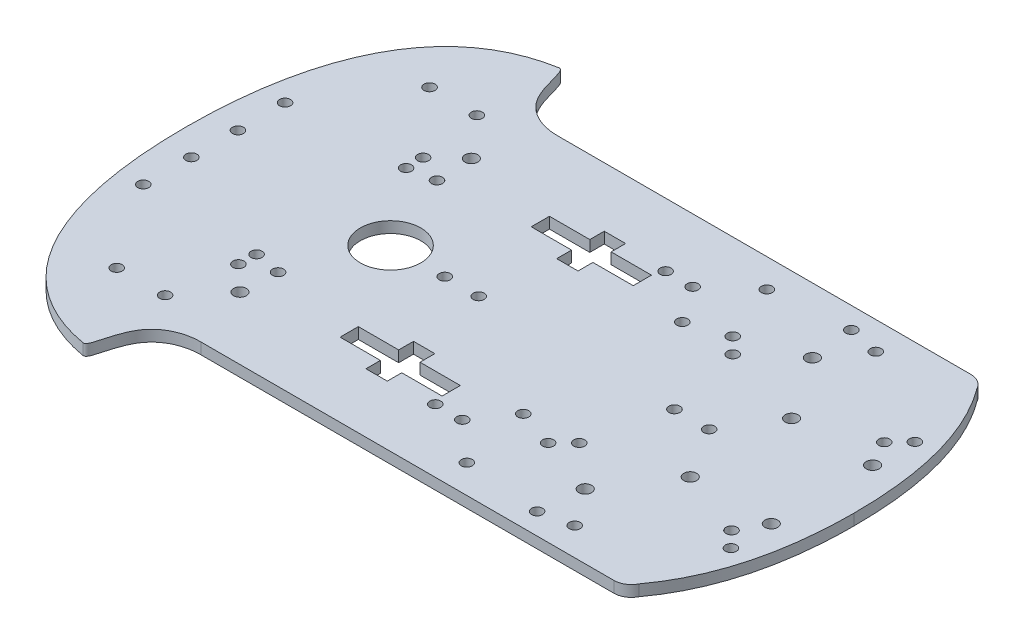
SolidWorks part; units mm, degrees
ref_plane "Front Plane" through (0, 0, 0) normal (0, 0, 1) x (1, 0, 0)
ref_plane "Top Plane" through (0, 0, 0) normal (0, 1, 0) x (1, 0, 0)
ref_plane "Right Plane" through (0, 0, 0) normal (1, 0, 0) x (0, 0, -1)
sketch "Sketch3" plane through (0, 0, 0) normal (0, 1, 0) x (1, 0, 0)
  line L0 (97.5968, 74.8054) -> (92.9104, -30.4241) construction
  line L1 (0, 0) -> (121.1912, 0) construction
  line L2 (11.94, 30.9929) -> (0, 30.9929)
  line L3 (11.94, -30.9929) -> (0, -30.9929)
  line L4 (0, 30.9929) -> (0, 25.5929)
  line L5 (0, -30.9929) -> (0, -25.5929)
  line L6 (0, 25.5929) -> (11.94, 25.5929)
  line L7 (0, -25.5929) -> (11.94, -25.5929)
  line L8 (11.94, 25.5929) -> (11.94, 21.1924)
  line L9 (11.94, -25.5929) -> (11.94, -21.1924)
  line L10 (11.94, 21.1924) -> (18.26, 21.1924)
  line L11 (11.94, -21.1924) -> (18.26, -21.1924)
  line L12 (18.26, 21.1924) -> (18.26, 25.5929)
  line L13 (18.26, -21.1924) -> (18.26, -25.5929)
  line L14 (18.26, 25.5929) -> (30.2, 25.5929)
  line L15 (18.26, -25.5929) -> (30.2, -25.5929)
  line L16 (30.2, 25.5929) -> (30.2, 30.9929)
  line L17 (30.2, -25.5929) -> (30.2, -30.9929)
  line L18 (30.2, 30.9929) -> (18.26, 30.9929)
  line L19 (30.2, -30.9929) -> (18.26, -30.9929)
  line L20 (18.26, 30.9929) -> (18.26, 35.2739)
  line L21 (18.26, -30.9929) -> (18.26, -35.2739)
  line L22 (18.26, 35.2739) -> (11.94, 35.2739)
  line L23 (18.26, -35.2739) -> (11.94, -35.2739)
  line L24 (11.94, 35.2739) -> (11.94, 30.9929)
  line L25 (11.94, -35.2739) -> (11.94, -30.9929)
  line L26 (0, 0) -> (-76.7012, 0) construction
  line L27 (87.6662, 15) -> (87.6662, -15) construction
  line L28 (87.6662, -15) -> (111.6662, -15) construction
  line L29 (111.6662, -15) -> (111.6662, 15) construction
  line L30 (111.6662, 15) -> (87.6662, 15) construction
  line L31 (31.2849, -34.0983) -> (39.2849, -34.0983) construction
  line L32 (-76.7012, 0) -> (-76.7012, -20.9854) construction
  line L33 (-36.6507, 70.4667) -> (-12.2251, 74.7655) construction
  line L34 (-19.4127, 52.8292) -> (102.905, 52.8292)
  line L35 (121.1912, 0) -> (121.1912, -12.7713) construction
  line L36 (-19.4127, -52.8292) -> (102.905, -52.8292)
  circle A0 centre (83.0358, 44.5617) radius 1.632
  circle A1 centre (83.0358, -44.5617) radius 1.632
  circle A2 centre (111.943, 27.2275) radius 1.632
  circle A3 centre (111.943, -27.2275) radius 1.632
  circle A4 centre (107.4976, 22.6103) radius 1.6319
  circle A5 centre (107.4976, -22.6103) radius 1.6319
  circle A6 centre (111.6662, 15) radius 1.8987
  circle A7 centre (111.6662, -15) radius 1.8987
  circle A8 centre (87.6662, 15) radius 1.8987
  circle A9 centre (87.6662, -15) radius 1.8987
  circle A10 centre (75.2051, 33.6273) radius 1.8987
  circle A11 centre (75.2051, -33.6273) radius 1.8987
  circle A12 centre (73.8468, 46.523) radius 1.6319
  circle A13 centre (73.8468, -46.523) radius 1.6319
  circle A14 centre (62.5335, 22.7171) radius 1.632
  circle A15 centre (62.5335, -22.7171) radius 1.632
  circle A16 centre (57.9166, 27.334) radius 1.6319
  circle A17 centre (57.9166, -27.334) radius 1.6319
  circle A18 centre (50.9457, 44.4144) radius 1.6319
  circle A19 centre (50.9457, -44.4144) radius 1.6319
  circle A20 centre (46.7819, 23.5346) radius 1.6319
  circle A21 centre (46.7819, -23.5346) radius 1.6319
  circle A22 centre (39.2849, 34.0983) radius 1.6319
  circle A23 centre (39.2849, -34.0983) radius 1.6319
  circle A24 centre (31.2849, 34.0983) radius 1.6319
  circle A25 centre (31.2849, -34.0983) radius 1.6319
  circle A26 centre (-26.3754, 34.2532) radius 1.8986
  circle A27 centre (-26.3754, -34.2532) radius 1.8986
  circle A28 centre (-25.8292, 23.5251) radius 1.632
  circle A29 centre (-25.8292, -23.5251) radius 1.632
  circle A30 centre (-33.591, 22.1292) radius 1.6319
  circle A31 centre (-33.591, -22.1292) radius 1.6319
  circle A32 centre (-36.6507, 46.1425) radius 1.6319
  circle A33 centre (-36.6507, -46.1425) radius 1.6319
  circle A34 centre (-50.8184, 46.3022) radius 1.6319
  circle A35 centre (-50.8184, -46.3022) radius 1.6319
  circle A36 centre (-68.2739, 20.9854) radius 1.6319
  circle A37 centre (-68.2739, -20.9854) radius 1.6319
  circle A38 centre (-68.129, 6.8968) radius 1.6319
  circle A39 centre (-68.129, -6.8968) radius 1.6319
  circle A40 centre (-16.053, 0) radius 8.9626
  circle A41 centre (10.0448, 0) radius 1.632
  circle A42 centre (68.0007, 0) radius 1.6319
  circle A43 centre (78.2719, 0) radius 1.632
  circle A44 centre (-33.7502, 27.334) radius 1.6319
  circle A45 centre (-33.7502, -27.334) radius 1.6319
  circle A46 centre (0, 0) radius 1.632
  arc A47 (102.905, 52.8292) -> (107.4976, 50.0246) centre (102.905, 47.6667) cw
  arc A48 (102.905, -52.8292) -> (107.4976, -50.0246) centre (102.905, -47.6667) ccw
  spline S0 degree 3 poles (-76.7012, 0) (-76.7012, 30.9297) (-68.7186, 64.823) (-36.6507, 70.4667) knots 0 0 0 0 1 1 1 1
  spline S1 degree 3 poles (-36.6507, 70.4667) (-34.7114, 70.8081) (-34.7249, 61.8258) (-27.6468, 54.4438) (-23.2508, 52.8292) (-19.4127, 52.8292) knots 0 0 0 0 0.592102 0.692102 1 1 1 1
  spline S2 degree 2 poles (107.4976, 50.0246) (121.1912, 31.5125) (121.1912, 0) knots 0 0 0 1 1 1
  spline S3 degree 2 poles (107.4976, -50.0246) (121.1912, -31.5125) (121.1912, 0) knots 0 0 0 1 1 1
  spline S4 degree 3 poles (-36.6507, -70.4667) (-34.7114, -70.8081) (-34.7249, -61.8258) (-27.6468, -54.4438) (-23.2508, -52.8292) (-19.4127, -52.8292) knots 0 0 0 0 0.592102 0.692102 1 1 1 1
  spline S5 degree 3 poles (-76.7012, 0) (-76.7012, -30.9297) (-68.7186, -64.823) (-36.6507, -70.4667) knots 0 0 0 0 1 1 1 1
  point P5 (46.7819, 23.5346)
  point P6 (46.7819, -23.5346)
  point P7 (57.9166, 27.334)
  point P8 (57.9166, -27.334)
  point P9 (62.5335, 22.7171)
  point P10 (62.5335, -22.7171)
  point P11 (75.2051, 33.6273)
  point P12 (75.2051, -33.6273)
  point P13 (87.6662, 15)
  point P14 (87.6662, -15)
  point P15 (83.0358, 44.5617)
  point P16 (83.0358, -44.5617)
  point P17 (73.8468, 46.523)
  point P18 (73.8468, -46.523)
  point P19 (111.943, 27.2275)
  point P20 (111.943, -27.2275)
  point P21 (107.4976, 22.6103)
  point P22 (107.4976, -22.6103)
  point P23 (111.6662, 15)
  point P24 (111.6662, -15)
  point P25 (-36.6507, 46.1425)
  point P26 (-36.6507, -46.1425)
  point P27 (-26.3754, 34.2532)
  point P28 (-26.3754, -34.2532)
  point P29 (-25.8292, 23.5251)
  point P30 (-25.8292, -23.5251)
  point P31 (-33.591, 22.1292)
  point P32 (-33.591, -22.1292)
  point P33 (-68.2739, 20.9854)
  point P34 (-68.2739, -20.9854)
  point P35 (-68.129, 6.8968)
  point P36 (-68.129, -6.8968)
  point P37 (-50.8184, 46.3022)
  point P38 (-50.8184, -46.3022)
  point P73 (50.9457, 44.4144)
  point P76 (50.9457, -44.4144)
  point P77 (39.2849, 34.0983)
  point P78 (39.2849, -34.0983)
  point P79 (31.2849, 34.0983)
  point P80 (31.2849, -34.0983)
  point P157 (-33.7502, 27.334)
  point P159 (-33.7502, -27.334)
  point P165 (111.6662, 0)
  dimension "D2" = 3.2639
  dimension "D3" = 3.7973
  dimension "D10" = 17.9253
  dimension "D55" = 5.1625
  dimension "D56" = 102.905
  dimension "D1" = 105.3338
  dimension "D4" = 30
  dimension "D5" = 24
  dimension "D6" = 8
  dimension "D7" = 5.4
  dimension "D8" = 30.2
  dimension "D9" = 6.32
  dimension "D11" = 10.0448
  dimension "D12" = 31.2849
  dimension "D13" = 46.7819
  dimension "D14" = 50.9457
  dimension "D15" = 57.9166
  dimension "D16" = 62.5335
  dimension "D17" = 68.0007
  dimension "D18" = 73.8468
  dimension "D19" = 75.2051
  dimension "D20" = 78.2719
  dimension "D21" = 83.0358
  dimension "D22" = 87.6662
  dimension "D23" = 107.4976
  dimension "D24" = 111.943
  dimension "D25" = 16.053
  dimension "D26" = 25.8292
  dimension "D27" = 26.3754
  dimension "D28" = 33.591
  dimension "D29" = 33.7502
  dimension "D30" = 36.6507
  dimension "D31" = 50.8184
  dimension "D32" = 68.129
  dimension "D33" = 68.2739
  dimension "D34" = 6.8968
  dimension "D35" = 20.9854
  dimension "D36" = 21.1924
  dimension "D37" = 22.1292
  dimension "D38" = 22.6103
  dimension "D39" = 22.7171
  dimension "D40" = 23.5251
  dimension "D41" = 23.5346
  dimension "D42" = 25.5929
  dimension "D43" = 27.2275
  dimension "D44" = 27.334
  dimension "D45" = 27.334
  dimension "D46" = 33.6273
  dimension "D47" = 34.0983
  dimension "D48" = 34.2532
  dimension "D49" = 35.2739
  dimension "D50" = 44.4144
  dimension "D51" = 44.5617
  dimension "D52" = 46.1425
  dimension "D53" = 46.3022
  dimension "D54" = 46.523
  dimension "D57" = 107.4976
  dimension "D58" = 121.1912
  dimension "D59" = 19.4127
  dimension "D60" = 29.8149
  dimension "D61" = 36.6507
  dimension "D62" = 76.7012
  dimension "D63" = 47.6667
  dimension "D64" = 56.7633
  dimension "D65" = 70.4667
  dimension "D71" = 20.9854
extrude "Boss-Extrude1" add sketch "Sketch3" along normal blind 3.3
